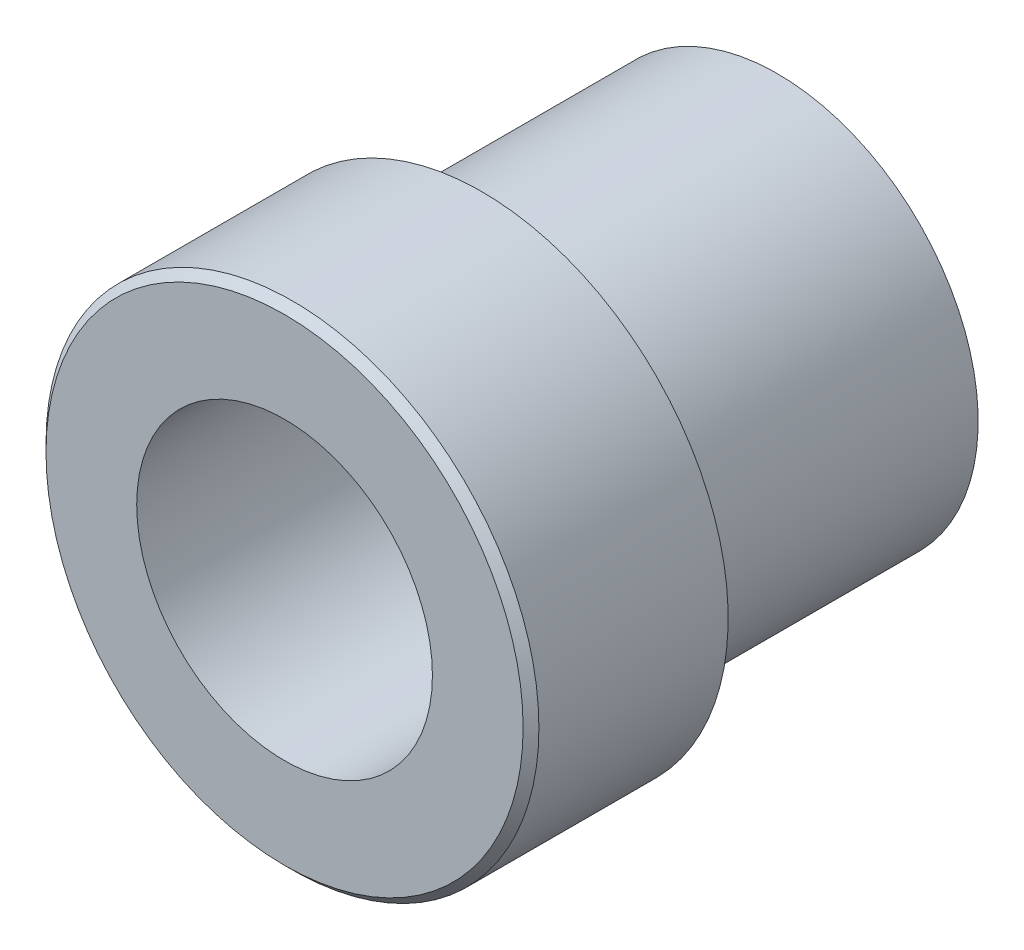
SolidWorks part; units mm, degrees
material "AISI 4130 Steel, annealed at 865C"
ref_plane "Front" through (0, 0, 0) normal (0, 0, 1) x (1, 0, 0)
ref_plane "Top" through (0, 0, 0) normal (0, 1, 0) x (1, 0, 0)
ref_plane "Right" through (0, 0, 0) normal (1, 0, 0) x (0, 0, -1)
sketch "Sketch1" plane through (0, 0, 0) normal (0, 0, 1) x (1, 0, 0)
  circle A0 centre (0, 0) radius 7.9375
  dimension "D1" = 15.875
extrude "Boss-Extrude1" add sketch "Sketch1" along normal blind 15.875
chamfer "Chamfer1" distance 0.254 angle 45 1 edges at (7.9375, 0, 15.875)
sketch "Sketch2" plane through (0, 0, 0) normal (0, 0, -1) x (-1, 0, 0)
  circle A0 centre (0, 0) radius 6.4643
  circle A1 centre (0, 0) radius 7.9375 construction
  dimension "D1" = 1.4732
extrude "Cut-Extrude1" cut sketch "Sketch2" against normal blind 9.525 flip side to cut
sketch "Sketch4" [suppressed] plane through (0, 0, 19.05) normal (0, 0, 1) x (1, 0, 0)
  line L1 (6.4158, 0) -> (3.2079, 5.5563)
  line L2 (3.2079, 5.5563) -> (-3.2079, 5.5563)
  line L3 (-3.2079, 5.5563) -> (-6.4158, 0)
  line L4 (-6.4158, 0) -> (-3.2079, -5.5563)
  line L5 (-3.2079, -5.5563) -> (3.2079, -5.5563)
  line L6 (3.2079, -5.5563) -> (6.4158, 0)
  circle A0 centre (0, 0) radius 5.5562 construction
  circle A1 centre (0, 0) radius 6.35 construction
  circle A2 centre (0, 0) radius 6.35
  dimension "D1" = 11.1125
extrude "Cut-Extrude3" [suppressed] cut sketch "Sketch4" against normal blind 5.5562
hole_wizard "Tap Drill for 3/8-24 Tap1" [suppressed] positions "Sketch5" profile "Sketch6" hole size "3/8-24" standard "ANSI Inch"
sketch "Sketch5" plane through (0, 0, 15.875) normal (0, 0, 1) x (1, 0, 0)
  point P0 (0, 0)
sketch "Sketch6" plane through (0, 0, 15.875) normal (1, 0, 0) x (0, -1, 0)
  line L0 (0, 0) -> (0, 15.875)
  line L1 (0, 15.875) -> (4.2164, 15.875)
  line L2 (4.2164, 15.875) -> (4.2164, 0)
  line L5 (4.2164, 0) -> (0, 0)
  line L11 (0, -6.35) -> (0, 107.95) construction
  dimension "Thru Hole Dia." = 8.4328
  dimension "Thru Hole Depth" = 15.875
hole_wizard "5/16 (0.3125) Dowel Hole1" positions "Sketch7" profile "Sketch8" hole size "5/16" standard "ANSI Inch" end condition through all
sketch "Sketch7" plane through (0, 0, 15.875) normal (0, 0, 1) x (1, 0, 0)
  point P0 (0, 0)
sketch "Sketch8" plane through (0, 0, 15.875) normal (1, 0, 0) x (0, -1, 0)
  line L0 (0, 0) -> (0, 15.875)
  line L1 (0, 15.875) -> (4.7625, 15.875)
  line L2 (4.7625, 15.875) -> (4.7625, 0)
  line L5 (4.7625, 0) -> (0, 0)
  line L11 (0, -6.35) -> (0, 107.95) construction
  dimension "Thru Hole Dia." = 9.525
  dimension "Thru Hole Depth" = 15.875
hole_wizard "Tap Drill for 1/4-28 Tap1" [suppressed] positions "Sketch9" profile "Sketch10" hole size "1/4-28" standard "ANSI Inch"
sketch "Sketch9" plane through (0, 0, 19.05) normal (0, 0, 1) x (1, 0, 0)
  point P0 (0, 0)
sketch "Sketch10" plane through (0, 0, 19.05) normal (1, 0, 0) x (0, -1, 0)
  line L0 (0, 0) -> (0, 19.05)
  line L1 (0, 19.05) -> (2.7051, 19.05)
  line L2 (2.7051, 19.05) -> (2.7051, 0)
  line L5 (2.7051, 0) -> (0, 0)
  line L11 (0, -6.35) -> (0, 107.95) construction
  dimension "Thru Hole Dia." = 5.4102
  dimension "Thru Hole Depth" = 19.05
equation "\"Tube Radius\"= 5 / 16in"
equation "\"Wall Thickness\"= 0.058"
equation "\"D1@Sketch1\"= 2 * \"Tube Radius\""
equation "\"D1@Sketch2\" = \"Wall Thickness\""
